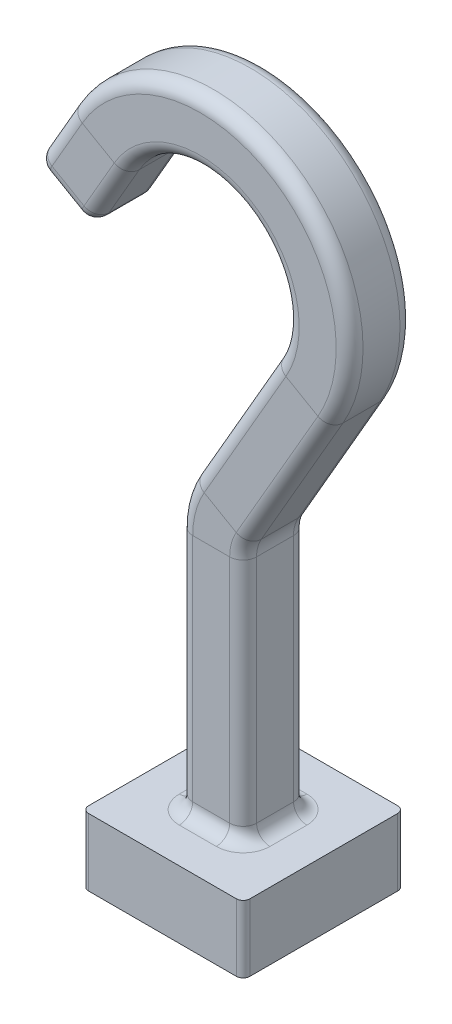
SolidWorks part; units mm, degrees
ref_plane "Front Plane" through (0, 0, 0) normal (0, 0, 1) x (1, 0, 0)
ref_plane "Top Plane" through (0, 0, 0) normal (0, 1, 0) x (1, 0, 0)
ref_plane "Right Plane" through (0, 0, 0) normal (1, 0, 0) x (0, 0, -1)
sketch "Sketch1" plane through (0, 0, 0) normal (0, 1, 0) x (1, 0, 0)
  line L1 (-12, -12) -> (12, -12)
  line L2 (-12, -12) -> (-12, 12)
  line L3 (-12, 12) -> (12, 12)
  line L4 (12, -12) -> (12, 12)
  line L5 (-12, -12) -> (12, 12) construction
  line L6 (-12, 12) -> (12, -12) construction
  point P0 (0, 0)
  dimension "D1" = 24
extrude "Boss-Extrude1" add sketch "Sketch1" along normal blind 10
sketch "Sketch2" plane through (0, 0, 0) normal (0, 0, 1) x (1, 0, 0)
  line L0 (0, 10) -> (0, 46.3205)
  line L1 (-12, 10) -> (12, 10) construction
  line L2 (1.3397, 51.3205) -> (13.5, 72.3827)
  line L3 (-16.8109, 89.8827) -> (-22.3109, 80.3564)
  arc A0 (13.5, 72.3827) -> (-16.8109, 89.8827) centre (-1.6554, 81.1327) ccw
  arc A1 (0, 46.3205) -> (1.3397, 51.3205) centre (10, 46.3205) cw
  point P11 (0, 49)
  dimension "D2" = 27
  dimension "D4" = 17.5
  dimension "D6" = 10
  dimension "D1" = 39
  dimension "D3" = 11
  dimension "D5" = 150
sketch "Sketch3" plane through (0, 10, 0) normal (0, 1, 0) x (1, 0, 0)
  line L1 (2.75, -4.75) -> (-2.75, -4.75)
  line L2 (4.75, -2.75) -> (4.75, 2.75)
  line L3 (2.75, 4.75) -> (-2.75, 4.75)
  line L4 (-4.75, -2.75) -> (-4.75, 2.75)
  line L5 (4.75, -4.75) -> (-4.75, 4.75) construction
  line L6 (4.75, 4.75) -> (-4.75, -4.75) construction
  arc A0 (-2.75, -4.75) -> (-4.75, -2.75) centre (-2.75, -2.75) cw
  arc A1 (2.75, -4.75) -> (4.75, -2.75) centre (2.75, -2.75) ccw
  arc A2 (4.75, 2.75) -> (2.75, 4.75) centre (2.75, 2.75) ccw
  arc A3 (-2.75, 4.75) -> (-4.75, 2.75) centre (-2.75, 2.75) ccw
  point P0 (0, 0)
  dimension "D2" = 2
  dimension "D1" = 9.5
sweep "Sweep1" add profiles "Sketch3" path "Sketch2"
fillet "Fillet1" radius 2 16 edges at (-18.7046, 78.2743, 4.1642) (-18.1973, 77.9814, 0) (-18.7046, 78.2743, -4.1642) (-22.3109, 80.3564, -4.75) (-25.9172, 82.4385, -4.1642) (-26.4245, 82.7314, 0) (-25.9172, 82.4385, 4.1642) (-22.3109, 80.3564, 4.75) (-4.1642, 10, 4.1642) (-4.75, 10, 0) (-4.1642, 10, -4.1642) (0, 10, -4.75) (4.1642, 10, -4.1642) (4.75, 10, 0) (4.1642, 10, 4.1642) (0, 10, 4.75)
fillet "Fillet2" radius 1 4 edges at (12, 5, 12) (-12, 5, -12) (12, 5, -12) (-12, 5, 12)
